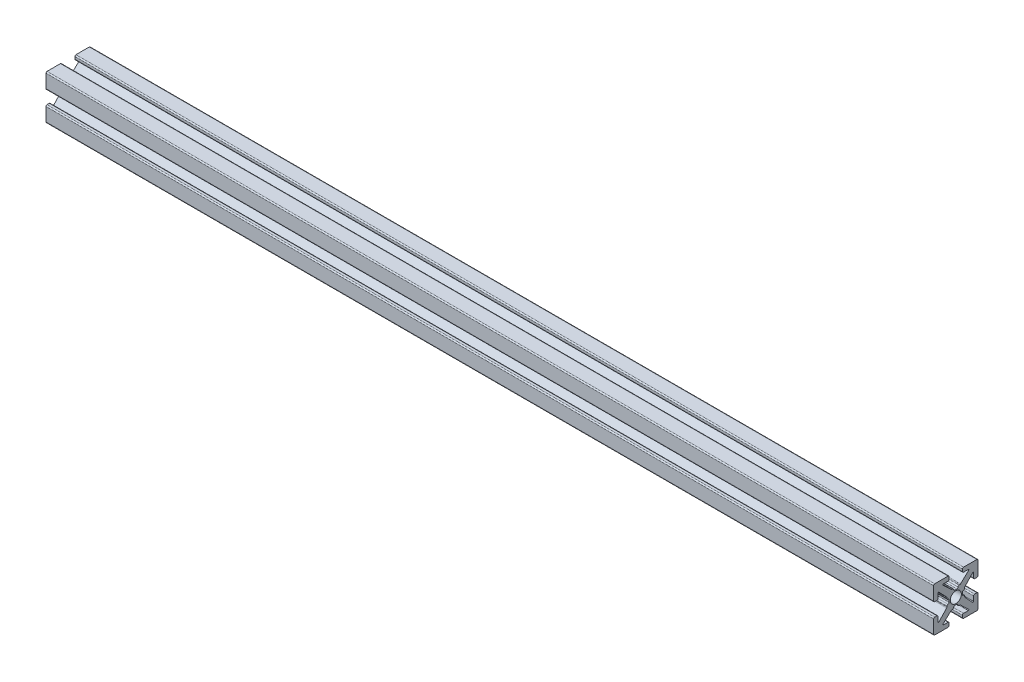
SolidWorks part; units mm, degrees
material "1060 Сплав"
ref_plane "Front Plane" through (0, 0, 0) normal (0, 0, 1) x (1, 0, 0)
ref_plane "Top Plane" through (0, 0, 0) normal (0, 1, 0) x (1, 0, 0)
ref_plane "Right Plane" through (0, 0, 0) normal (1, 0, 0) x (0, 0, -1)
sketch "Sketch1" plane through (0, 0, 0) normal (1, 0, 0) x (0, 0, -1)
  line L0 (0, 0) -> (0, 1.4948) construction
  line L1 (-0.2413, 1.4948) -> (0.2413, 1.4948)
  line L2 (5, 1.7526) -> (5, 4.746)
  line L3 (0.7493, 2.0028) -> (0.8899, 2.0028)
  line L4 (1.0639, 2.0718) -> (2.8908, 3.7899)
  line L5 (2.8038, 4.0094) -> (1.7526, 4.0094)
  line L6 (1.4986, 4.2634) -> (1.4986, 4.746)
  line L7 (1.7526, 5) -> (4.746, 5)
  line L8 (5, 5) -> (0, 0) construction
  line L9 (0, 0) -> (8.6271, 0) construction
  line L10 (0, 0) -> (0, 5) construction
  line L11 (4.2634, 1.4986) -> (4.746, 1.4986)
  line L12 (4.0094, 2.8038) -> (4.0094, 1.7526)
  line L13 (2.0718, 1.0639) -> (3.7899, 2.8908)
  line L14 (2.0028, 0.7493) -> (2.0028, 0.8899)
  line L15 (1.4948, -0.2413) -> (1.4948, 0.2413)
  line L16 (0, 0) -> (1.4948, 0) construction
  line L17 (-0.2413, -1.4948) -> (0.2413, -1.4948)
  line L18 (0.7493, -2.0028) -> (0.8899, -2.0028)
  line L19 (1.0639, -2.0718) -> (2.8908, -3.7899)
  line L20 (2.8038, -4.0094) -> (1.7526, -4.0094)
  line L21 (1.4986, -4.2634) -> (1.4986, -4.746)
  line L22 (1.7526, -5) -> (4.746, -5)
  line L23 (5, -1.7526) -> (5, -4.746)
  line L24 (4.2634, -1.4986) -> (4.746, -1.4986)
  line L25 (4.0094, -2.8038) -> (4.0094, -1.7526)
  line L26 (2.0718, -1.0639) -> (3.7899, -2.8908)
  line L27 (2.0028, -0.7493) -> (2.0028, -0.8899)
  line L28 (-0.7493, 2.0028) -> (-0.8899, 2.0028)
  line L29 (-1.0639, 2.0718) -> (-2.8908, 3.7899)
  line L30 (-2.8038, 4.0094) -> (-1.7526, 4.0094)
  line L31 (-1.4986, 4.2634) -> (-1.4986, 4.746)
  line L32 (-1.7526, 5) -> (-4.746, 5)
  line L33 (-5, 1.7526) -> (-5, 4.746)
  line L34 (-4.2634, 1.4986) -> (-4.746, 1.4986)
  line L35 (-4.0094, 2.8038) -> (-4.0094, 1.7526)
  line L36 (-2.0718, 1.0639) -> (-3.7899, 2.8908)
  line L37 (-2.0028, 0.7493) -> (-2.0028, 0.8899)
  line L38 (-1.4948, -0.2413) -> (-1.4948, 0.2413)
  line L39 (-2.0028, -0.7493) -> (-2.0028, -0.8899)
  line L40 (-2.0718, -1.0639) -> (-3.7899, -2.8908)
  line L41 (-4.0094, -2.8038) -> (-4.0094, -1.7526)
  line L42 (-4.2634, -1.4986) -> (-4.746, -1.4986)
  line L43 (-5, -1.7526) -> (-5, -4.746)
  line L44 (-1.7526, -5) -> (-4.746, -5)
  line L45 (-1.4986, -4.2634) -> (-1.4986, -4.746)
  line L46 (-2.8038, -4.0094) -> (-1.7526, -4.0094)
  line L47 (-1.0639, -2.0718) -> (-2.8908, -3.7899)
  line L48 (-0.7493, -2.0028) -> (-0.8899, -2.0028)
  arc A0 (2.8908, 3.7899) -> (2.8038, 4.0094) centre (2.8038, 3.8824) ccw
  arc A1 (0.4953, 1.7488) -> (0.7493, 2.0028) centre (0.7493, 1.7488) cw
  arc A2 (0.8899, 2.0028) -> (1.0639, 2.0718) centre (0.8899, 2.2568) ccw
  arc A3 (1.7526, 4.0094) -> (1.4986, 4.2634) centre (1.7526, 4.2634) cw
  arc A4 (1.4986, 4.746) -> (1.7526, 5) centre (1.7526, 4.746) cw
  arc A5 (0.2413, 1.4948) -> (0.4953, 1.7488) centre (0.2413, 1.7488) ccw
  arc A6 (4.746, 1.4986) -> (5, 1.7526) centre (4.746, 1.7526) ccw
  arc A7 (4.0094, 1.7526) -> (4.2634, 1.4986) centre (4.2634, 1.7526) ccw
  arc A8 (3.7899, 2.8908) -> (4.0094, 2.8038) centre (3.8824, 2.8038) cw
  arc A9 (2.0028, 0.8899) -> (2.0718, 1.0639) centre (2.2568, 0.8899) cw
  arc A10 (1.7488, 0.4953) -> (2.0028, 0.7493) centre (1.7488, 0.7493) ccw
  arc A11 (1.4948, 0.2413) -> (1.7488, 0.4953) centre (1.7488, 0.2413) cw
  arc A12 (0.2413, -1.4948) -> (0.4953, -1.7488) centre (0.2413, -1.7488) cw
  arc A13 (0.4953, -1.7488) -> (0.7493, -2.0028) centre (0.7493, -1.7488) ccw
  arc A14 (0.8899, -2.0028) -> (1.0639, -2.0718) centre (0.8899, -2.2568) cw
  arc A15 (2.8908, -3.7899) -> (2.8038, -4.0094) centre (2.8038, -3.8824) cw
  arc A16 (1.7526, -4.0094) -> (1.4986, -4.2634) centre (1.7526, -4.2634) ccw
  arc A17 (1.4986, -4.746) -> (1.7526, -5) centre (1.7526, -4.746) ccw
  arc A18 (4.746, -1.4986) -> (5, -1.7526) centre (4.746, -1.7526) cw
  arc A19 (4.0094, -1.7526) -> (4.2634, -1.4986) centre (4.2634, -1.7526) cw
  arc A20 (3.7899, -2.8908) -> (4.0094, -2.8038) centre (3.8824, -2.8038) ccw
  arc A21 (2.0028, -0.8899) -> (2.0718, -1.0639) centre (2.2568, -0.8899) ccw
  arc A22 (1.7488, -0.4953) -> (2.0028, -0.7493) centre (1.7488, -0.7493) cw
  arc A23 (1.4948, -0.2413) -> (1.7488, -0.4953) centre (1.7488, -0.2413) ccw
  arc A24 (-0.2413, 1.4948) -> (-0.4953, 1.7488) centre (-0.2413, 1.7488) cw
  arc A25 (-0.4953, 1.7488) -> (-0.7493, 2.0028) centre (-0.7493, 1.7488) ccw
  arc A26 (-0.8899, 2.0028) -> (-1.0639, 2.0718) centre (-0.8899, 2.2568) cw
  arc A27 (-2.8908, 3.7899) -> (-2.8038, 4.0094) centre (-2.8038, 3.8824) cw
  arc A28 (-1.7526, 4.0094) -> (-1.4986, 4.2634) centre (-1.7526, 4.2634) ccw
  arc A29 (-1.4986, 4.746) -> (-1.7526, 5) centre (-1.7526, 4.746) ccw
  arc A30 (-4.746, 1.4986) -> (-5, 1.7526) centre (-4.746, 1.7526) cw
  arc A31 (-4.0094, 1.7526) -> (-4.2634, 1.4986) centre (-4.2634, 1.7526) cw
  arc A32 (-3.7899, 2.8908) -> (-4.0094, 2.8038) centre (-3.8824, 2.8038) ccw
  arc A33 (-2.0028, 0.8899) -> (-2.0718, 1.0639) centre (-2.2568, 0.8899) ccw
  arc A34 (-1.7488, 0.4953) -> (-2.0028, 0.7493) centre (-1.7488, 0.7493) cw
  arc A35 (-1.4948, 0.2413) -> (-1.7488, 0.4953) centre (-1.7488, 0.2413) ccw
  arc A36 (-1.4948, -0.2413) -> (-1.7488, -0.4953) centre (-1.7488, -0.2413) cw
  arc A37 (-1.7488, -0.4953) -> (-2.0028, -0.7493) centre (-1.7488, -0.7493) ccw
  arc A38 (-2.0028, -0.8899) -> (-2.0718, -1.0639) centre (-2.2568, -0.8899) cw
  arc A39 (-3.7899, -2.8908) -> (-4.0094, -2.8038) centre (-3.8824, -2.8038) cw
  arc A40 (-4.0094, -1.7526) -> (-4.2634, -1.4986) centre (-4.2634, -1.7526) ccw
  arc A41 (-4.746, -1.4986) -> (-5, -1.7526) centre (-4.746, -1.7526) ccw
  arc A42 (-1.4986, -4.746) -> (-1.7526, -5) centre (-1.7526, -4.746) cw
  arc A43 (-1.7526, -4.0094) -> (-1.4986, -4.2634) centre (-1.7526, -4.2634) cw
  arc A44 (-2.8908, -3.7899) -> (-2.8038, -4.0094) centre (-2.8038, -3.8824) ccw
  arc A45 (-0.8899, -2.0028) -> (-1.0639, -2.0718) centre (-0.8899, -2.2568) ccw
  arc A46 (-0.4953, -1.7488) -> (-0.7493, -2.0028) centre (-0.7493, -1.7488) cw
  arc A47 (-0.2413, -1.4948) -> (-0.4953, -1.7488) centre (-0.2413, -1.7488) ccw
  arc A48 (-4.746, 5) -> (-5, 4.746) centre (-4.746, 4.746) ccw
  arc A49 (-5, -4.746) -> (-4.746, -5) centre (-4.746, -4.746) ccw
  arc A50 (4.746, -5) -> (5, -4.746) centre (4.746, -4.746) ccw
  arc A51 (4.746, 5) -> (5, 4.746) centre (4.746, 4.746) cw
  point P14 (3.1242, 4.0094)
  point P19 (0.9906, 2.0028)
  point P150 (0, -1.4948)
  point P152 (-5, 5)
  point P155 (-5, -5)
  point P158 (5, -5)
  dimension "D10" = 0.127
  dimension "D11" = 0.254
  dimension "D2" = 0.254
  dimension "D1" = 10
  dimension "D3" = 2.9972
  dimension "D4" = 0.508
  dimension "D5" = 2.9972
  dimension "D6" = 0.9906
  dimension "D7" = 1.6256
  dimension "D8" = 1.9812
  dimension "D9" = 0.9906
extrude "Estrusione-Estrusione1" add sketch "Sketch1" along normal blind 200 contours L36 A32 L35 A31 L34 A30 L33 A48 L32 A29 L31 A28 L30 A27 L29 A26 L28 A25 A24 L1 A5 A1 L3 A2 L4 A0 L5 A3 L6 A4 L7 A51 L2 A6 L11 A7 L12 A8 L13 A9 L14 A10 A11 L15 A23 A22 L27 A21 L26 A20 L25 A19 L24 A18 L23 A50 L22 A17 L21 A16 L20 A15 L19 A14 L18 A13 A12 L17 A47 A46 L48 A45 L47 A44 L46 A43 L45 A42 L44 A49 L43 A41 L42 A40 L41 A39 L40 A38 L39 A37 A36 L38 A35 A34 L37 A33
hole_wizard "Foro filettato M3x0.5-1" positions "Schizzo2" profile "Schizzo1" tap size "M3x0.5" standard "Ansi Metric" end condition through all
sketch "Schizzo2" plane through (0, 0, 0) normal (-1, 0, 0) x (0, 0, 1)
  point P0 (0, 0)
sketch "Schizzo1" plane through (0, 0, 0) normal (0, 1, 0) x (0, 0, 1)
  line L0 (0, 0) -> (0, 200)
  line L1 (0, 200) -> (1.25, 200)
  line L2 (1.25, 200) -> (1.25, 0)
  line L5 (1.25, 0) -> (0, 0)
  line L11 (0, -6.35) -> (0, 107.95) construction
  dimension "Thread Major Dia." = 2.5
  dimension "Thru Tap Drill Depth" = 200
equation "\"D1@Estrusione-Estrusione1\"= \"camera plate width\" - 20"
equation "\"camera plate width\"=220"
equation "\"camera plate length\"=220"
